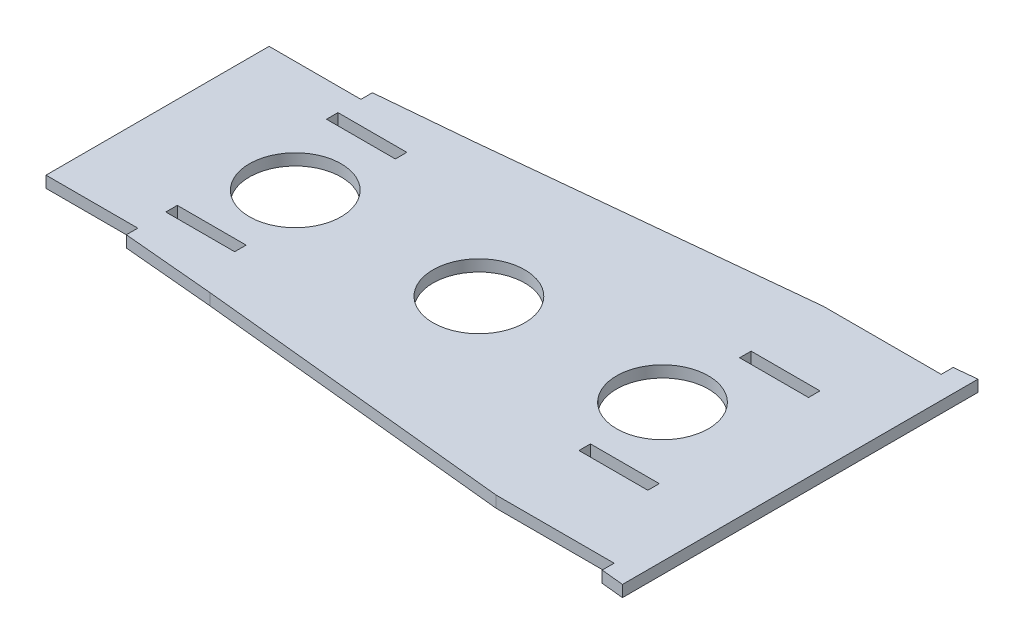
SolidWorks part; units mm, degrees
material "Balsa"
ref_plane "Front Plane" through (0, 0, 0) normal (0, 0, 1) x (1, 0, 0)
ref_plane "Top Plane" through (0, 0, 0) normal (0, 1, 0) x (1, 0, 0)
ref_plane "Right Plane" through (0, 0, 0) normal (1, 0, 0) x (0, 0, -1)
sketch "Sketch1" plane through (0, 0, 0) normal (0, 1, 0) x (1, 0, 0)
  line L0 (-63.5, 36.3216) -> (-63.5, -36.3216)
  line L1 (-63.5, -36.3216) -> (63.5, -49.1808)
  line L2 (-114.3, -31.75) -> (-114.3, 31.75)
  line L3 (-63.5, 36.3216) -> (63.5, 49.1808)
  line L4 (63.5, -49.1808) -> (63.5, 49.1808)
  line L5 (0, 42.7512) -> (0, -42.7512) construction
  line L6 (-63.5, 0) -> (63.5, 0) construction
  line L7 (-114.3, 31.75) -> (-63.5, 36.3216)
  line L8 (-114.3, -31.75) -> (-63.5, -36.3216)
  line L9 (-114.3, 30.8608) -> (-88.9, 30.8608)
  line L10 (-88.9, 30.8608) -> (-88.9, 34.0358)
  line L11 (24.6454, 45.2466) -> (57.2568, 45.2466)
  line L12 (57.2568, 45.2466) -> (57.2568, 48.5486)
  line L13 (57.2568, -45.2466) -> (57.2568, -48.5486)
  line L14 (24.6454, -45.2466) -> (57.2568, -45.2466)
  line L15 (-114.3, -30.8608) -> (-88.9, -30.8608)
  line L16 (-88.9, -30.8608) -> (-88.9, -34.0358)
  point P0 (0, 0)
  dimension "D1" = 72.6432
  dimension "D2" = 98.3615
  dimension "D3" = 50.8
  dimension "D4" = 63.5
  dimension "D5" = 3.175
  dimension "D6" = 127
  dimension "D7" = 3.302
  dimension "D8" = 6.2432
  dimension "D9" = 25.4
extrude "Boss-Extrude2" add sketch "Sketch1" along normal blind 3.175 contours L2 L8 L0 L7 | L1 L4 L3 L0
sketch "Sketch6" plane through (0, 3.175, 0) normal (0, 1, 0) x (1, 0, 0)
  line L0 (-114.3, 0) -> (63.5, 0) construction
  line L1 (-114.3, -30.8608) -> (-114.3, 30.8608) construction
  line L2 (63.5, -49.1808) -> (63.5, 49.1808) construction
  line L3 (-25.4, 0) -> (-25.4, 40.1793) construction
  line L4 (-63.5, 36.3216) -> (24.6454, 45.2466) construction
  line L5 (-114.3, 30.8608) -> (-88.9, 30.8608) construction
  line L6 (-88.9, 24.5108) -> (-69.85, 24.5108)
  line L7 (-88.9, 24.5108) -> (-88.9, 21.3358)
  line L8 (-88.9, 21.3358) -> (-69.85, 21.3358)
  line L9 (-69.85, 24.5108) -> (-69.85, 21.3358)
  dimension "D1" = 3.175
  dimension "D2" = 19.05
  dimension "D3" = 6.35
  dimension "D4" = 25.4
extrude "Cut-Extrude5" cut sketch "Sketch6" against normal up to surface (3.175 mm away) up to face at (-19.1176, 0, 0)
pattern_linear "LPattern1" count 2 spacing 114.3 along (1, 0, 0) count 2 spacing 44.45 along (0, 0, 1) of "Cut-Extrude5"
sketch "Sketch7" plane through (0, 3.175, 0) normal (0, 1, 0) x (1, 0, 0)
  line L0 (-114.3, 0) -> (63.5, 0) construction
  line L1 (-114.3, -30.8608) -> (-114.3, 30.8608) construction
  line L2 (63.5, -49.1808) -> (63.5, 49.1808) construction
  circle A0 centre (-25.4, 0) radius 12.7
  dimension "D1" = 25.4
extrude "Cut-Extrude6" cut sketch "Sketch7" against normal up to surface (3.175 mm away) up to face at (34.925, 0, -22.9233)
pattern_linear "LPattern2" count 2 spacing 50.8 along (-1, 0, 0) count 2 spacing 50.8 along (1, 0, 0) of "Cut-Extrude6"
